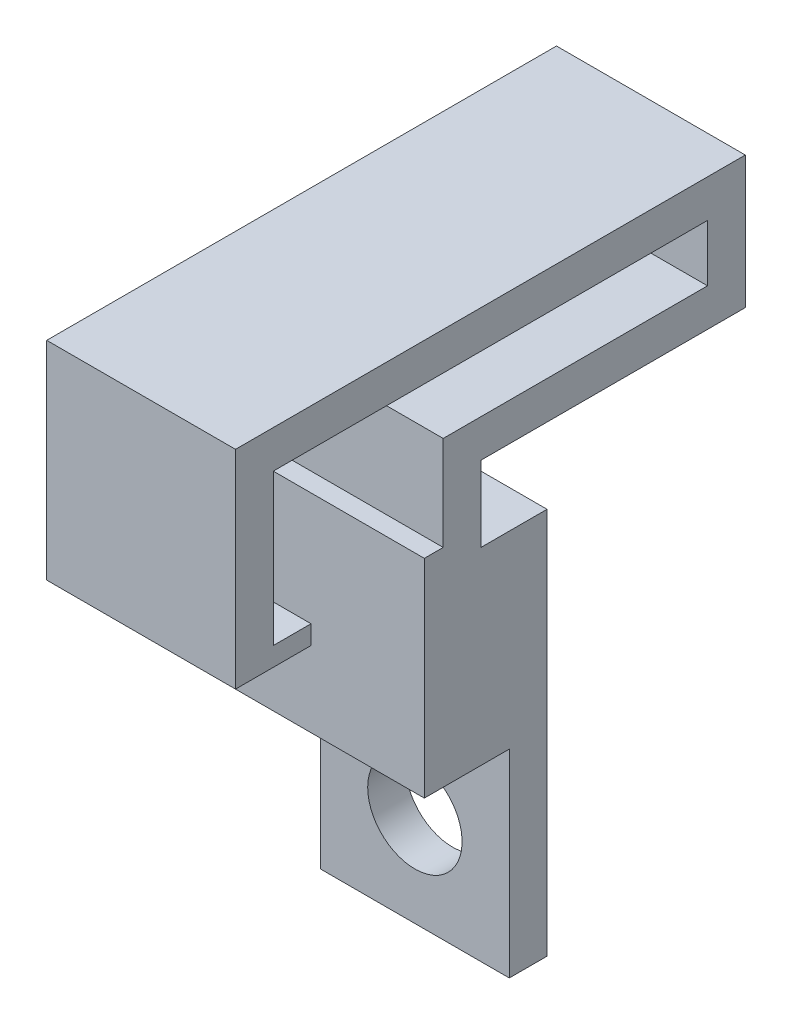
SolidWorks part; units mm, degrees
ref_plane "Plan de face" through (0, 0, 0) normal (0, 0, 1) x (1, 0, 0)
ref_plane "Plan de dessus" through (0, 0, 0) normal (0, 1, 0) x (1, 0, 0)
ref_plane "Plan de droite" through (0, 0, 0) normal (1, 0, 0) x (0, 0, -1)
sketch "Esquisse1" plane through (0, 0, 0) normal (0, 0, 1) x (1, 0, 0)
  line L1 (0, 0) -> (-10, 0)
  line L2 (0, 0) -> (0, 10)
  line L3 (0, 10) -> (-10, 10)
  line L4 (-10, 0) -> (-10, 10)
  dimension "D1" = 10
  dimension "D2" = 10
extrude "Boss.-Extru.1" add sketch "Esquisse1" along normal blind 2
sketch "Esquisse2" plane through (0, 10, 0) normal (0, 1, 0) x (1, 0, 0)
  line L0 (0, -2) -> (0, 0) construction
  line L1 (-10, 0) -> (0, 0)
  line L2 (-10, 0) -> (-10, -1)
  line L3 (-10, -1) -> (0, -1)
  line L4 (0, 0) -> (0, -1)
  dimension "D1" = 1
extrude "Boss.-Extru.2" add sketch "Esquisse2" along normal blind 5
sketch "Esquisse3" plane through (0, 0, 0) normal (0, 0, -1) x (-1, 0, 0)
  line L0 (10, 15) -> (10, 0) construction
  line L1 (0, 15) -> (10, 15)
  line L2 (0, 15) -> (0, 14)
  line L3 (0, 14) -> (10, 14)
  line L4 (10, 15) -> (10, 14)
  dimension "D1" = 1
extrude "Boss.-Extru.3" add sketch "Esquisse3" along normal blind 14
sketch "Esquisse4" plane through (0, 15, 0) normal (0, 1, 0) x (1, 0, 0)
  line L0 (0, -1) -> (0, 14) construction
  line L1 (-10, 14) -> (0, 14)
  line L2 (-10, 14) -> (-10, 13)
  line L3 (-10, 13) -> (0, 13)
  line L4 (0, 14) -> (0, 13)
  dimension "D1" = 1
extrude "Boss.-Extru.4" add sketch "Esquisse4" along normal blind 4
sketch "Esquisse5" plane through (0, 14, 0) normal (0, -1, 0) x (1, 0, 0)
  line L1 (0, -14) -> (-10, -14)
  line L2 (0, -14) -> (0, 0)
  line L3 (0, 0) -> (-10, 0)
  line L4 (-10, -14) -> (-10, 0)
extrude "Boss.-Extru.5" add sketch "Esquisse5" along normal blind 1
sketch "Esquisse6" plane through (0, 0, 0) normal (0, 0, -1) x (-1, 0, 0)
  line L1 (0, 13) -> (10, 13)
  line L2 (0, 13) -> (0, 0)
  line L3 (0, 0) -> (10, 0)
  line L4 (10, 13) -> (10, 0)
extrude "Boss.-Extru.6" add sketch "Esquisse6" along normal blind 1
sketch "Esquisse7" plane through (0, 0, -13) normal (0, 0, 1) x (1, 0, 0)
  line L0 (0, 19) -> (0, 15) construction
  line L1 (-10, 19) -> (0, 19)
  line L2 (-10, 19) -> (-10, 18)
  line L3 (-10, 18) -> (0, 18)
  line L4 (0, 19) -> (0, 18)
  dimension "D1" = 1
extrude "Boss.-Extru.7" add sketch "Esquisse7" along normal blind 24
sketch "Esquisse8" plane through (0, 18, 0) normal (0, -1, 0) x (1, 0, 0)
  line L0 (0, 11) -> (0, -13) construction
  line L1 (-10, 11) -> (0, 11)
  line L2 (-10, 11) -> (-10, 10)
  line L3 (-10, 10) -> (0, 10)
  line L4 (0, 11) -> (0, 10)
  dimension "D1" = 1
extrude "Boss.-Extru.8" add sketch "Esquisse8" along normal blind 9
sketch "Esquisse9" plane through (0, 19, 0) normal (0, 1, 0) x (1, 0, 0)
  line L0 (0, -11) -> (0, 14) construction
  line L1 (-10, 14) -> (0, 14)
  line L2 (-10, 14) -> (-10, -11)
  line L3 (-10, -11) -> (0, -11)
  line L4 (0, 14) -> (0, -11)
  dimension "D1" = 25
extrude "Boss.-Extru.9" add sketch "Esquisse9" along normal blind 1
sketch "Esquisse10" plane through (0, 0, -14) normal (0, 0, -1) x (-1, 0, 0)
  line L1 (0, 13) -> (10, 13)
  line L2 (0, 13) -> (0, 20)
  line L3 (0, 20) -> (10, 20)
  line L4 (10, 13) -> (10, 20)
extrude "Boss.-Extru.10" add sketch "Esquisse10" along normal blind 1
sketch "Esquisse13" plane through (0, 0, 11) normal (0, 0, 1) x (1, 0, 0)
  line L1 (-10, 20) -> (0, 20)
  line L2 (-10, 20) -> (-10, 9)
  line L3 (-10, 9) -> (0, 9)
  line L4 (0, 20) -> (0, 9)
extrude "Boss.-Extru.13" add sketch "Esquisse13" along normal blind 1
sketch "Esquisse14" plane through (0, 0, 10) normal (0, 0, -1) x (-1, 0, 0)
  line L0 (10, 9) -> (10, 18) construction
  line L1 (0, 9) -> (10, 9)
  line L2 (0, 9) -> (0, 10)
  line L3 (0, 10) -> (10, 10)
  line L4 (10, 9) -> (10, 10)
  dimension "D1" = 1
extrude "Boss.-Extru.14" add sketch "Esquisse14" along normal blind 2
sketch "Esquisse15" plane through (-10, 0, 0) normal (-1, 0, 0) x (0, 0, 1)
  line L0 (12, 20) -> (12, 9) construction
  line L1 (-15, 20) -> (12, 20)
  line L2 (-15, 20) -> (-15, 18)
  line L3 (-15, 18) -> (12, 18)
  line L4 (12, 20) -> (12, 18)
  line L5 (12, 9) -> (8, 9) construction
  line L6 (-15, 13) -> (-13.0046, 13)
  line L7 (-15, 13) -> (-15, 20)
  line L8 (-15, 20) -> (-13.0046, 20)
  line L9 (-13.0046, 13) -> (-13.0046, 20)
  line L10 (1, 15) -> (-15, 15)
  line L11 (1, 15) -> (1, 13)
  line L12 (1, 13) -> (-15, 13)
  line L13 (-15, 15) -> (-15, 13)
  line L14 (1, 15) -> (-1, 15)
  line L15 (1, 15) -> (1, 0)
  line L16 (1, 0) -> (-1, 0)
  line L17 (-1, 15) -> (-1, 0)
  line L18 (2, 10) -> (1, 10)
  line L19 (2, 10) -> (2, 0)
  line L20 (2, 0) -> (1, 0)
  line L21 (1, 10) -> (1, 0)
  line L22 (12, 20) -> (10, 20)
  line L23 (12, 20) -> (12, 9)
  line L24 (12, 9) -> (10, 9)
  line L25 (10, 20) -> (10, 9)
  line L27 (8, 10) -> (10, 10)
  line L28 (8, 10) -> (8, 9)
  line L29 (8, 9) -> (10, 9)
  line L30 (10, 10) -> (10, 9)
  line M10 (-1, 13) -> (-1, 0)
  line M11 (-1, 0) -> (2, 0)
  line M12 (2, 0) -> (2, 10)
  line M13 (2, 10) -> (1, 10)
  line M14 (1, 10) -> (1, 15)
  line M15 (1, 15) -> (-13, 15)
  line M17 (-13, 18) -> (10, 18)
  line M18 (10, 18) -> (10, 10)
  line M19 (10, 10) -> (8, 10)
  line M20 (8, 10) -> (8, 9)
  line M21 (8, 9) -> (12, 9)
  line M22 (12, 9) -> (12, 20)
  line M23 (12, 20) -> (-15, 20)
  line M24 (-15, 20) -> (-15, 13)
  line M25 (-15, 13) -> (-1, 13)
  dimension "D1" = 2
  dimension "D2" = 1.9954
extrude "Boss.-Extru.15" add sketch "Esquisse15" along normal blind 40 contours L25 L1 L9 L3 M17 | L3 L9 L1 M24 | L10 L9 L3 M24 | L9 L10 L7 M25 | L17 L10 L9 M25 | L17 L12 M15 M14 | L15 L12 M14 M10 M11 | L15 M13 M11 M12 | L25 L3 M18 M21 M22 | L25 L3 M23 M22 | L25 M19 M20 M21
sketch "Esquisse16" plane through (0, 0, 0) normal (0, -1, 0) x (1, 0, 0)
  line L1 (0, -1) -> (-50, -1)
  line L2 (0, -1) -> (0, 2)
  line L3 (0, 2) -> (-50, 2)
  line L4 (-50, -1) -> (-50, 2)
extrude "Boss.-Extru.16" add sketch "Esquisse16" along normal blind 1
sketch "Esquisse17" plane through (0, 0, -1) normal (0, 0, -1) x (-1, 0, 0)
  line L0 (50, 13) -> (50, -1) construction
  line L1 (0, -1) -> (50, -1)
  line L2 (0, -1) -> (0, 9)
  line L3 (0, 9) -> (50, 9)
  line L4 (50, -1) -> (50, 9)
  dimension "D1" = 10
extrude "Boss.-Extru.17" add sketch "Esquisse17" along normal blind 3.5
sketch "Esquisse19" plane through (0, -1, 0) normal (0, -1, 0) x (-1, 0, 0)
  line L0 (50, -2) -> (50, 4.5) construction
  line L1 (0, 4.5) -> (50, 4.5)
  line L2 (0, 4.5) -> (0, 2.5)
  line L3 (0, 2.5) -> (50, 2.5)
  line L4 (50, 4.5) -> (50, 2.5)
  dimension "D1" = 2
extrude "Boss.-Extru.18" add sketch "Esquisse19" along normal blind 10.5
sketch "Esquisse20" plane through (-50, 0, 0) normal (-1, 0, 0) x (0, 0, 1)
  line L1 (-4.5, 9) -> (-2.5, 9)
  line L2 (-4.5, 9) -> (-4.5, -11.5)
  line L3 (-4.5, -11.5) -> (-2.5, -11.5)
  line L4 (-2.5, 9) -> (-2.5, -11.5)
  line L5 (2, -1) -> (-4.5, -1)
  line L6 (2, -1) -> (2, 9)
  line L7 (2, 9) -> (-4.5, 9)
  line L8 (-4.5, -1) -> (-4.5, 9)
  line L9 (2, 10) -> (-1, 10)
  line L10 (2, 10) -> (2, 9)
  line L11 (2, 9) -> (-1, 9)
  line L12 (-1, 10) -> (-1, 9)
  line L13 (1, 15) -> (-1, 15)
  line L14 (1, 15) -> (1, 10)
  line L15 (1, 10) -> (-1, 10)
  line L16 (-1, 15) -> (-1, 10)
  line L17 (-15, 13) -> (1, 13)
  line L18 (-15, 13) -> (-15, 15)
  line L19 (-15, 15) -> (1, 15)
  line L20 (1, 13) -> (1, 15)
  line L21 (-15, 13) -> (-13.0046, 13)
  line L22 (-15, 13) -> (-15, 18)
  line L23 (-15, 18) -> (-13.0046, 18)
  line L24 (-13.0046, 13) -> (-13.0046, 18)
  line L25 (12, 20) -> (-15, 20)
  line L26 (12, 20) -> (12, 18)
  line L27 (12, 18) -> (-15, 18)
  line L28 (-15, 20) -> (-15, 18)
  line L29 (12, 9) -> (10, 9)
  line L30 (12, 9) -> (12, 18)
  line L31 (12, 18) -> (10, 18)
  line L32 (10, 9) -> (10, 18)
  line L33 (8, 10) -> (12, 10)
  line L34 (8, 10) -> (8, 9)
  line L35 (8, 9) -> (12, 9)
  line L36 (12, 10) -> (12, 9)
  line M1 (-13.0046, 18) -> (10, 18)
  line M2 (10, 18) -> (10, 10)
  line M3 (10, 10) -> (8, 10)
  line M4 (8, 10) -> (8, 9)
  line M5 (8, 9) -> (12, 9)
  line M6 (12, 9) -> (12, 20)
  line M7 (12, 20) -> (-15, 20)
  line M8 (-15, 20) -> (-15, 13)
  line M9 (-15, 13) -> (-1, 13)
  line M10 (-1, 13) -> (-1, 9)
  line M11 (-1, 9) -> (-4.5, 9)
  line M12 (-4.5, 9) -> (-4.5, -11.5)
  line M13 (-4.5, -11.5) -> (-2.5, -11.5)
  line M14 (-2.5, -11.5) -> (-2.5, -1)
  line M15 (-2.5, -1) -> (2, -1)
  line M16 (2, -1) -> (2, 10)
  line M17 (2, 10) -> (1, 10)
  line M18 (1, 10) -> (1, 15)
  line M19 (1, 15) -> (-13.0046, 15)
  line M20 (-13.0046, 15) -> (-13.0046, 18)
extrude "Enlèv. mat.-Extru.1" cut sketch "Esquisse20" against normal blind 40 contours L5 L2 M14 M13 | L5 L4 M11 M12 | L7 L4 M16 M11 M15 | L17 L9 M10 M18 | L9 L7 M17 M10 M16 | L16 L17 L14 M19 | L24 L17 L16 M19 | L24 L19 M9 M8 | L23 L19 M8 M20 | L27 L23 M6 M7 M8 M1 | L33 L30 L27 M2 | L33 L32 M5 M6 | L32 M5 M3 M4
sketch "Esquisse21" plane through (0, 0, -4.5) normal (0, 0, -1) x (-1, 0, 0)
  line L0 (0, 9) -> (0, -11.5) construction
  line L1 (10, -11.5) -> (0, -11.5) construction
  circle A0 centre (5, -6.5) radius 2.5
  dimension "D1" = 5
  dimension "D2" = 5
  dimension "D3" = 5
extrude "Enlèv. mat.-Extru.2" cut sketch "Esquisse21" against normal blind 40
